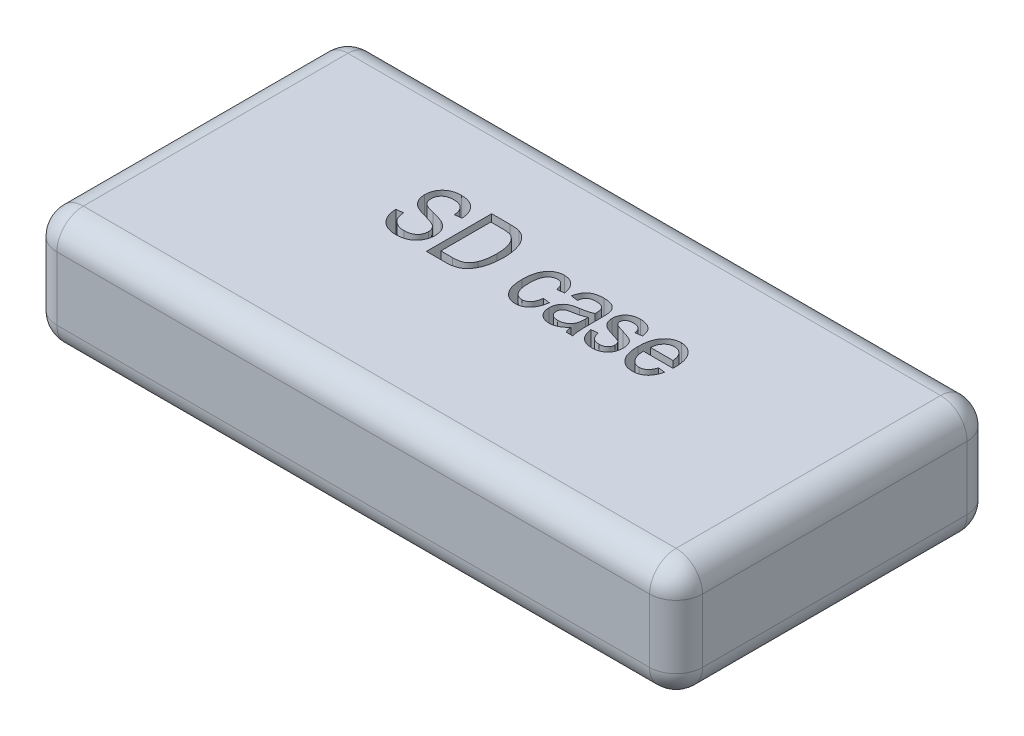
SolidWorks part; units mm, degrees
ref_plane "Front Plane" through (0, 0, 0) normal (0, 0, 1) x (1, 0, 0)
ref_plane "Top Plane" through (0, 0, 0) normal (0, 1, 0) x (1, 0, 0)
ref_plane "Right Plane" through (0, 0, 0) normal (1, 0, 0) x (0, 0, -1)
sketch "Sketch1" plane through (0, 0, 0) normal (0, 1, 0) x (1, 0, 0)
  line L0 (-4.7857, -30) -> (117.2143, -30) construction
  line L1 (-4.7857, 0) -> (117.2143, 0)
  line L2 (-4.7857, 0) -> (-4.7857, -60)
  line L3 (-4.7857, -60) -> (117.2143, -60)
  line L4 (117.2143, 0) -> (117.2143, -60)
  dimension "D1" = 122
  dimension "D2" = 60
extrude "Boss-Extrude1" add sketch "Sketch1" along normal blind 22
fillet "Fillet1" radius 5 12 edges at (-4.7857, 11, 60) (117.2143, 11, 60) (117.2143, 11, 0) (-4.7857, 11, 0) (56.2143, 22, 0) (117.2143, 22, 30) (56.2143, 22, 60) (-4.7857, 22, 30) (56.2143, 0, 60) (117.2143, 0, 30) (56.2143, 0, 0) (-4.7857, 0, 30)
sketch "Sketch2" plane through (0, 22, 0) normal (0, 1, 0) x (1, 0, 0)
  line L0 (0.2143, -30) -> (112.2143, -30) construction
  line L1 (0.2143, -5) -> (0.2143, -55) construction
  line L2 (112.2143, -55) -> (112.2143, -5) construction
  text T0 "SD case" font "Arial Narrow" height in points 48
extrude "Cut-Extrude1" cut sketch "Sketch2" against normal through all
